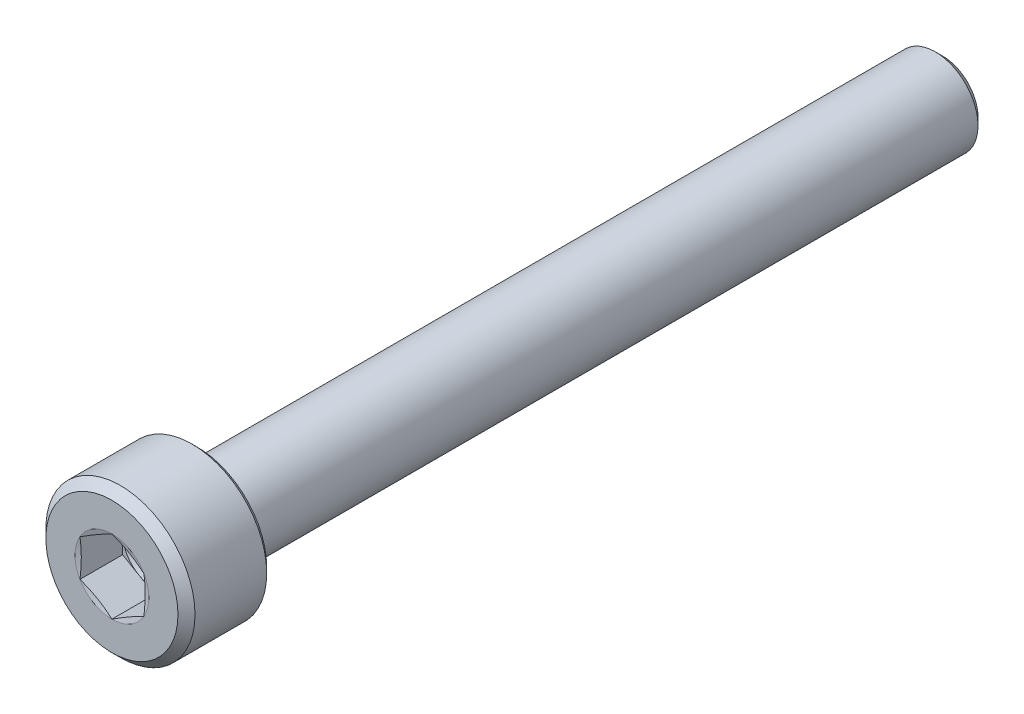
SolidWorks part; units mm, degrees
ref_plane "Front Plane" through (0, 0, 0) normal (0, 0, 1) x (1, 0, 0)
ref_plane "Top Plane" through (0, 0, 0) normal (0, 1, 0) x (1, 0, 0)
ref_plane "Right Plane" through (0, 0, 0) normal (1, 0, 0) x (0, 0, -1)
sketch "Sketch1" plane through (0, 0, 0) normal (1, 0, 0) x (0, 0, -1)
  line L0 (0, 0) -> (12.9407, 0) construction
  line L1 (0, 0) -> (0, 3.1)
  line L2 (0, 3.1) -> (0.4, 3.5)
  line L3 (0.4, 3.5) -> (3.765, 3.5)
  line L4 (4, 3.265) -> (4, 2.35)
  line L5 (4.6, 2) -> (38.65, 2)
  line L6 (38.65, 2) -> (39, 1.65)
  line L7 (39, 1.65) -> (39, 0)
  line L8 (39, 0) -> (0, 0)
  line L9 (3.765, 3.5) -> (4, 3.265)
  line L10 (4.5298, 2.0127) -> (4.1298, 2.1627)
  arc A2 (4.6, 2) -> (4.5298, 2.0127) centre (4.6, 2.2) cw
  arc A3 (4.1298, 2.1627) -> (4, 2.35) centre (4.2, 2.35) cw
  point P6 (4, 3.5)
  dimension "R2" = 0.2
  dimension "R1" = 0.2
  dimension "D1" = 45
  dimension "DK" = 7
  dimension "D3" = 45
  dimension "length" = 35
  dimension "K" = 4
  dimension "V" = 0.4
  dimension "HOLESIZE" = 4
  dimension "D4" = 3.3
  dimension "D5" = 45
  dimension "DW" = 6.53
  dimension "F" = 0.6
  dimension "DA" = 4.7
revolve "Revolve1" add sketch "Sketch1" angle 360 about L0
cosmetic thread "Cosmetic Thread1" parameters "D1"=20, "D2"=4
sketch "Sketch2" plane through (0, 0, 0) normal (0, 0, 1) x (1, 0, 0)
  line L0 (0, 0) -> (0, 1.7321) construction
  line L2 (0, 1.7321) -> (-1.5, 0.866)
  line L3 (-1.5, 0.866) -> (-1.5, -0.866)
  line L4 (-1.5, -0.866) -> (0, -1.7321)
  line L5 (0, -1.7321) -> (1.5, -0.866)
  line L6 (1.5, -0.866) -> (1.5, 0.866)
  line L7 (1.5, 0.866) -> (0, 1.7321)
  circle A0 centre (0, 0) radius 1.5 construction
  dimension "S" = 3
extrude "Cut-Extrude1" cut sketch "Sketch2" against normal blind 2
sketch "Sketch3" plane through (0, 0, 0) normal (1, 0, 0) x (0, 0, -1)
  line L0 (2, 0) -> (39, 0) construction
  line L1 (39, -1.65) -> (39, 1.65) construction
  line L2 (2, 0) -> (2, 1.5)
  line L4 (2, 1.5) -> (2.866, 0)
  line L5 (2.866, 0) -> (2, 0)
  line L6 (0, 3.1) -> (0, -3.1) construction
  dimension "DRILLANG" = 60
  dimension "DRILL DEPTH" = 2
  dimension "S2" = 3
revolve "Cut-Revolve2" cut sketch "Sketch3" angle 360 about L0
sketch "Sketch4" plane through (0, 0, 0) normal (1, 0, 0) x (0, 0, -1)
  line L0 (0, 0) -> (4.6121, 0) construction
  line L1 (0, 1.7321) -> (0, 1.5)
  line L2 (0, 3.1) -> (0, -3.1) construction
  line L3 (0, 1.5) -> (0.0622, 1.5)
  line L4 (0.0622, 1.5) -> (0, 1.7321)
  point P12 (0.0311, 1.5)
  dimension "D1" = 3
  dimension "D2" = 15
revolve "Cut-Revolve3" cut sketch "Sketch4" angle 360 about L0
